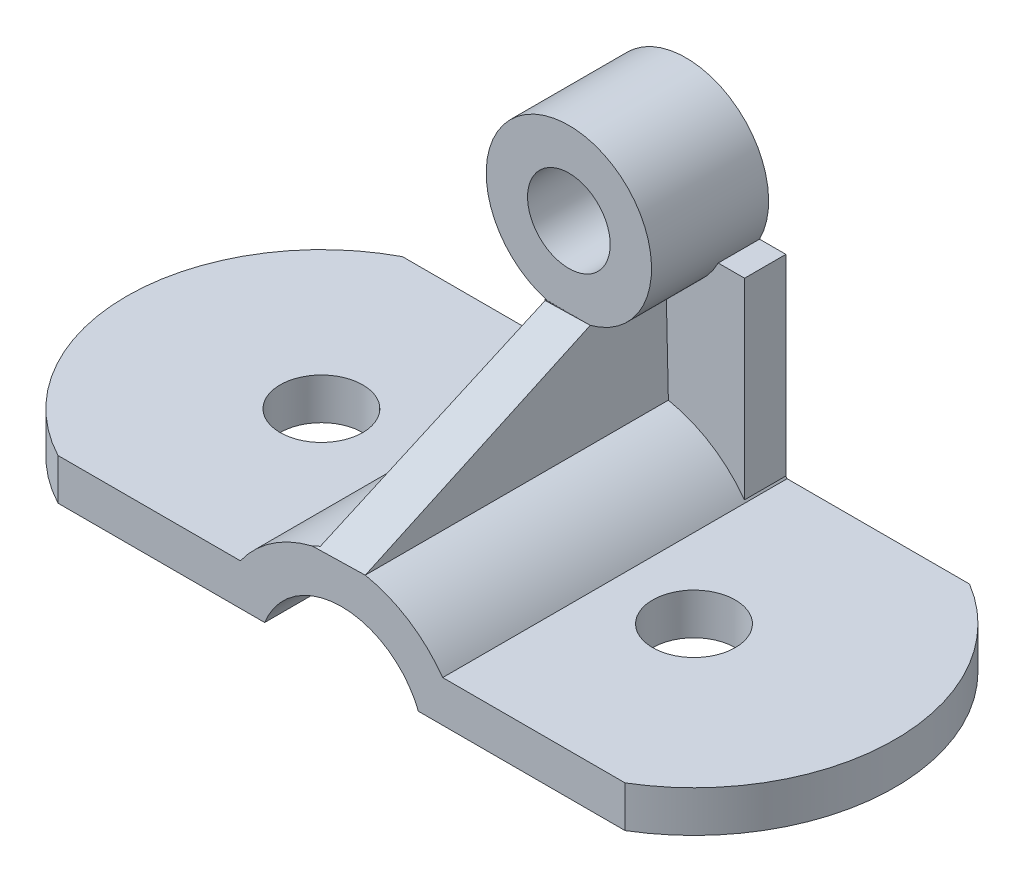
SolidWorks part; units mm, degrees
ref_plane "Front Plane" through (0, 0, 0) normal (0, 0, 1) x (1, 0, 0)
ref_plane "Top Plane" through (0, 0, 0) normal (0, 1, 0) x (1, 0, 0)
ref_plane "Right Plane" through (0, 0, 0) normal (1, 0, 0) x (0, 0, -1)
sketch "Sketch1" plane through (0, 0, 0) normal (0, 0, 1) x (1, 0, 0)
  line L0 (0, 0) -> (-60, 0)
  line L1 (44.6374, 0) -> (104.6374, 0)
  line L2 (-60, 0) -> (-60, 12)
  line L3 (-60, 12) -> (-7.0468, 12)
  line L4 (104.6374, 0) -> (104.6374, 12)
  line L5 (104.6374, 12) -> (51.6842, 12)
  arc A0 (0, 0) -> (44.6374, 0) centre (22.3187, -8.8247) cw
  arc A3 (51.6842, 12) -> (-7.0468, 12) centre (22.3187, -8.8247) ccw
  point P4 (0, 0)
  dimension "D2" = 24
  dimension "D5" = 36
  dimension "D1" = 60
  dimension "D3" = 60
  dimension "D4" = 12
extrude "Boss-Extrude2" add sketch "Sketch1" along normal blind 100
sketch "Sketch2" plane through (0, 0, 0) normal (0, 1, 0) x (1, 0, 0)
  line L0 (-33.5234, -100) -> (-33.5234, 0) construction
  line L1 (-7.0468, -100) -> (-60, -100) construction
  line L2 (-7.0468, 0) -> (-60, 0) construction
  line L4 (74.6374, -100) -> (74.6374, 0) construction
  line L7 (44.6374, -100) -> (104.6374, -100) construction
  circle A0 centre (-33.5234, -50) radius 12
  circle A1 centre (74.6374, -50) radius 12
  dimension "D1" = 24
  dimension "D2" = 24
extrude "Cut-Extrude2" cut sketch "Sketch2" along normal blind 100
sketch "Sketch3" plane through (0, 0, 0) normal (0, 1, 0) x (1, 0, 0)
  line L0 (-33.5234, -100) -> (-33.5234, 0) construction
  line L1 (-7.0468, -100) -> (-60, -100) construction
  line L2 (-7.0468, 0) -> (-60, 0) construction
  line L3 (104.6374, -100) -> (104.6374, 0) construction
  line L4 (-60, 0) -> (-60, -100)
  line L5 (104.6374, 0) -> (104.6374, -100)
  arc A0 (-60, -100) -> (-60, 0) centre (-33.5234, -50) cw
  arc A1 (104.6374, -100) -> (104.6374, 0) centre (74.6374, -50) ccw
extrude "Boss-Extrude3" add sketch "Sketch3" along normal blind 12
sketch "Sketch4" plane through (0, 0, 0) normal (0, 0, 1) x (1, 0, 0)
  line L0 (22.3187, -8.8247) -> (22.3187, 79.1753) construction
  circle A0 centre (22.3187, 79.1753) radius 12
  circle A1 centre (22.3187, 79.1753) radius 24
  dimension "D2" = 24
  dimension "D3" = 48
  dimension "D1" = 88
extrude "Boss-Extrude4" add sketch "Sketch4" along normal blind 34 separate body
ref_plane "Plane2" through (-1.6813, 0, 0) normal (-1, 0, 0) x (0, 0, 1)
sketch "Sketch9" plane through (-1.6813, 0, 0) normal (-1, 0, 0) x (0, 0, 1)
  line L0 (0, 103.1753) -> (0, 55.1753) construction
  line L1 (0, 68.2352) -> (12, 68.2352)
  line L2 (0, 68.2352) -> (0, 12)
  line L3 (0, 12) -> (12, 12)
  line L4 (12, 68.2352) -> (12, 12)
  line L5 (100, 12) -> (0, 12) construction
  dimension "D1" = 12
extrude "Boss-Extrude14" add sketch "Sketch9" against normal blind 53
sketch "Sketch13" plane through (0, 0, 0) normal (0, 0, 1) x (1, 0, 0)
  arc A0 (15.4308, 56.1849) -> (28.5244, 55.9915) centre (22.3187, 79.1753) ccw
  arc A1 (0.9572, 68.2352) -> (43.6802, 68.2352) centre (22.3187, 79.1753) ccw construction
  point P3 (0, 0)
sketch "Sketch15" plane through (0, 0, 0) normal (0, 0, 1) x (1, 0, 0)
  line L0 (15.4308, 26.5102) -> (29.2066, 26.5102)
  line L1 (29.2066, 26.5102) -> (28.5244, 55.9915)
  line L2 (15.4308, 26.5102) -> (15.4308, 56.1849)
  line L3 (28.5244, 55.9915) -> (15.4308, 55.9915)
  arc A0 (51.6842, 12) -> (-7.0468, 12) centre (22.3187, -8.8247) ccw construction
  arc A1 (51.3187, 12.506) -> (-1.6813, 18.0081) centre (22.3187, -8.8247) ccw construction
extrude "Boss-Extrude15" add sketch "Sketch15" along normal blind 100 contours L1 L3 L2 L0
sketch "Sketch16" plane through (29.8041, 0.6897, 0) normal (0.9997, 0.0231, 0) x (0, 0, -1)
  line L0 (-34, 55.3166) -> (-100, 25.8275)
  line L4 (-100, 25.8275) -> (-100, 55.3166)
  line L6 (-100, 55.3166) -> (-101.7156, 69.7018)
  line L7 (-101.7156, 69.7018) -> (-35.1587, 67.5241)
  line L8 (-35.1587, 67.5241) -> (-34, 55.3166)
extrude "Cut-Extrude5" cut sketch "Sketch16" against normal blind 100
ref_plane "Plane3" through (27.2497, 68.2352, 12) normal (-1, 0, 0) x (0, 0, 1)
sketch "Sketch18" plane through (0, 68.2352, 0) normal (0, 1, 0) x (1, 0, 0)
  line L1 (17.3877, 0) -> (28.0188, 0)
  line L2 (17.3877, 0) -> (17.3877, -16.964)
  line L3 (17.3877, -16.964) -> (28.0188, -16.964)
  line L4 (28.0188, 0) -> (28.0188, -16.964)
extrude "Cut-Extrude6" cut sketch "Sketch18" against normal blind 2
